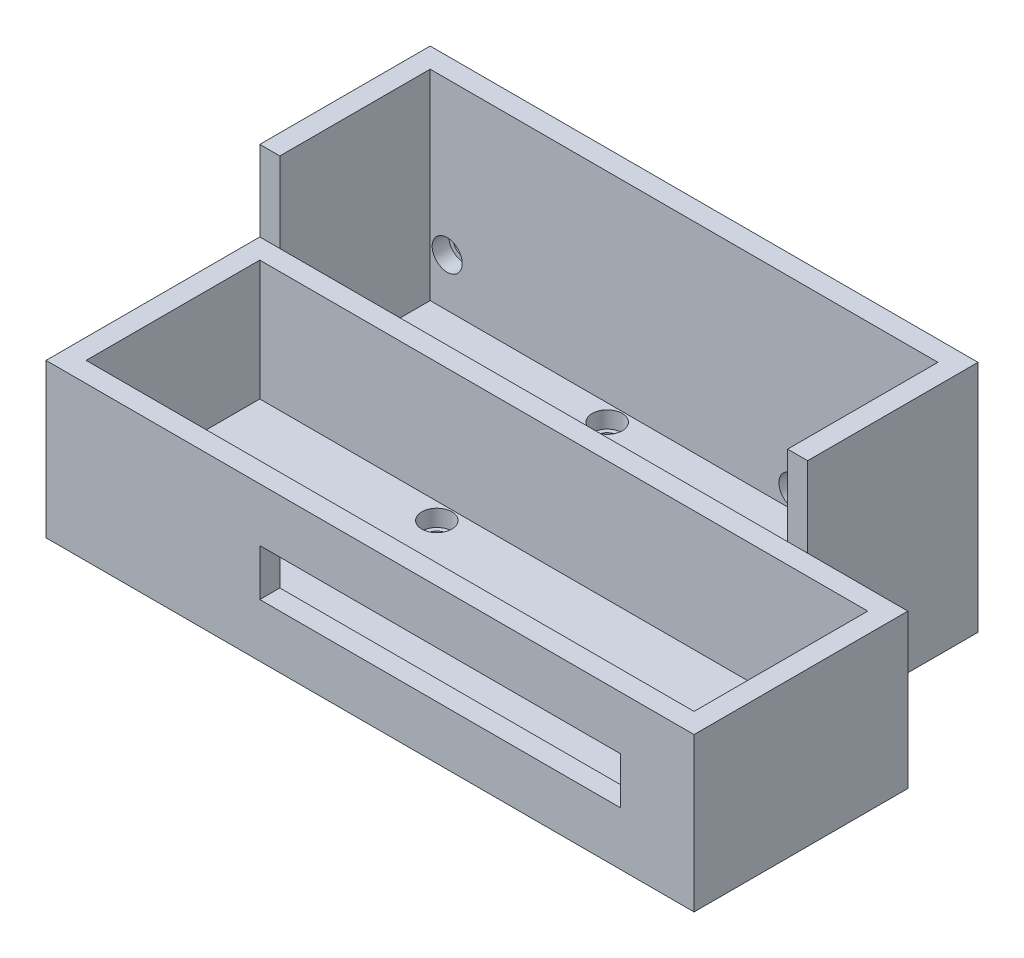
SolidWorks part; units mm, degrees
ref_plane "Front Plane" through (0, 0, 0) normal (0, 0, 1) x (1, 0, 0)
ref_plane "Top Plane" through (0, 0, 0) normal (0, 1, 0) x (1, 0, 0)
ref_plane "Right Plane" through (0, 0, 0) normal (1, 0, 0) x (0, 0, -1)
sketch "Sketch1" plane through (0, 0, 0) normal (0, 1, 0) x (1, 0, 0)
  line L1 (0, 0) -> (91, 0)
  line L2 (0, 0) -> (0, 26)
  line L3 (0, 26) -> (91, 26)
  line L4 (91, 0) -> (91, 26)
extrude "Boss-Extrude1" add sketch "Sketch1" along normal blind 5
sketch "Sketch2" plane through (0, 5, 0) normal (0, 1, 0) x (1, 0, 0)
  line L0 (0, 2.5) -> (29, 2.5) construction
  line L9 (29, 2.5) -> (29, 26) construction
  line L10 (91, 26) -> (0, 26) construction
  line L11 (29, 26) -> (29, 23.5) construction
  circle A0 centre (2.5, 2.5) radius 2.25
  circle A1 centre (88.5, 2.5) radius 2.25
  circle A2 centre (29, 23.5) radius 2.25
  dimension "D1" = 4.5
  dimension "D2" = 4.5
  dimension "D3" = 4.5
extrude "Cut-Extrude1" cut sketch "Sketch2" against normal blind 2.5
sketch "Sketch4" plane through (0, 2.5, 0) normal (0, 1, 0) x (1, 0, 0)
  circle A0 centre (2.5, 2.5) radius 1.6
  circle A1 centre (29, 23.5) radius 1.6
  circle A2 centre (88.5, 2.5) radius 1.6
  dimension "D1" = 3.2
  dimension "D2" = 3.2
  dimension "D3" = 3.2
extrude "Cut-Extrude3" cut sketch "Sketch4" against normal through all
sketch "Sketch5" plane through (0, 0, 0) normal (0, -1, 0) x (1, 0, 0)
  line L0 (-3, 0) -> (-3, -29) construction
  line L9 (-3, -29) -> (91, -29) construction
  line L10 (94, 3) -> (94, -26) construction
  line L11 (94, 3) -> (0, 3) construction
  line L13 (94, 3) -> (-3, 3)
  line L14 (94, 3) -> (94, -29)
  line L15 (94, -29) -> (-3, -29)
  line L16 (-3, 3) -> (-3, -29)
  line L17 (0, 0) -> (91, 0)
  line L18 (0, 0) -> (0, -26)
  line L19 (0, -26) -> (91, -26)
  line L20 (91, 0) -> (91, -26)
extrude "Boss-Extrude2" add sketch "Sketch5" against normal blind 23
sketch "Sketch6" plane through (0, 0, 3) normal (0, 0, 1) x (1, 0, 0)
  line L0 (-3, 0) -> (0, 0) construction
  line L1 (0, 0) -> (29, 0) construction
  line L2 (94, 0) -> (-3, 0) construction
  line L3 (29, 0) -> (83, 0) construction
  line L4 (83, 0) -> (83, 8) construction
  line L5 (83, 8) -> (83, 15) construction
  line L6 (83, 15) -> (29, 15) construction
  line L8 (29, 15) -> (83, 15)
  line L9 (29, 15) -> (29, 8)
  line L10 (29, 8) -> (83, 8)
  line L11 (83, 15) -> (83, 8)
  dimension "D1" = 8
  dimension "D2" = 7
extrude "Cut-Extrude4" cut sketch "Sketch6" against normal up to next
sketch "Sketch9" plane through (0, 0, -29) normal (0, 0, -1) x (-1, 0, 0)
  line L1 (0, 0) -> (-76, 0)
  line L2 (0, 0) -> (0, 5)
  line L3 (0, 5) -> (-76, 5)
  line L4 (-76, 0) -> (-76, 5)
extrude "Boss-Extrude3" add sketch "Sketch9" along normal blind 22.5
sketch "Sketch10" plane through (0, 5, 0) normal (0, 1, 0) x (1, 0, 0)
  line L0 (29, 23.5) -> (29, 49) construction
  circle A0 centre (29, 49) radius 2.25
  dimension "D1" = 4.5
extrude "Cut-Extrude5" cut sketch "Sketch10" against normal blind 2.5
sketch "Sketch11" plane through (0, 2.5, 0) normal (0, 1, 0) x (1, 0, 0)
  circle A0 centre (29, 49) radius 1.6
  dimension "D1" = 3.2
extrude "Cut-Extrude6" cut sketch "Sketch11" against normal through all
sketch "Sketch12" plane through (0, 0, 0) normal (0, -1, 0) x (1, 0, 0)
  line L1 (0, -29) -> (-3, -29)
  line L2 (0, -29) -> (0, -51.5)
  line L3 (0, -54.5) -> (-3, -54.5)
  line L4 (-3, -29) -> (-3, -54.5)
  line L5 (0, -54.5) -> (79, -54.5)
  line L7 (0, -51.5) -> (76, -51.5)
  line L8 (79, -54.5) -> (79, -51.5)
  line L10 (79, -51.5) -> (79, -29)
  line L11 (79, -29) -> (76, -29)
  line L12 (76, -51.5) -> (76, -29)
extrude "Boss-Extrude4" add sketch "Sketch12" against normal blind 35
sketch "Sketch13" plane through (79, 0, 0) normal (1, 0, 0) x (0, 0, -1)
  line L0 (29, 0) -> (31.5, 0) construction
  line L1 (54.5, 0) -> (29, 0) construction
  line L2 (31.5, 0) -> (31.5, 10) construction
  circle A0 centre (31.5, 10) radius 1.6
  dimension "D1" = 3.2
extrude "Cut-Extrude7" cut sketch "Sketch13" against normal up to next
sketch "Sketch14" plane through (0, 0, -54.5) normal (0, 0, -1) x (-1, 0, 0)
  line L0 (0, 0) -> (0, 5) construction
  line L1 (0, 5) -> (-76, 5) construction
  line L2 (-38, 5) -> (-38, 7.5) construction
  line L4 (-2.55, 7.5) -> (-2.55, 12.2) construction
  circle A0 centre (-54.45, 7.5) radius 1.6
  circle A1 centre (-2.55, 12.2) radius 1.6
  point P9 (-38, 7.5)
  dimension "D1" = 3.2
  dimension "D2" = 3.2
  dimension "D4" = 5.1
  dimension "D3" = 51.9
extrude "Cut-Extrude8" cut sketch "Sketch14" against normal up to next
sketch "Sketch16" plane through (0, 0, -51.5) normal (0, 0, 1) x (1, 0, 0)
  circle A0 centre (2.55, 12.2) radius 2.25
  circle A1 centre (54.45, 7.5) radius 2.25
  dimension "D1" = 4.5
  dimension "D2" = 4.5
extrude "Cut-Extrude10" cut sketch "Sketch16" against normal blind 2.5
sketch "Sketch17" plane through (0, 0, -54.5) normal (0, 0, -1) x (-1, 0, 0)
  circle A0 centre (-54.45, 7.5) radius 1.6
  circle A1 centre (-54.45, 7.5) radius 2.5
  circle A2 centre (-2.55, 12.2) radius 1.6
  circle A3 centre (-2.55, 12.2) radius 2.5
  dimension "D1" = 3.2
  dimension "D2" = 5
  dimension "D3" = 3.2
  dimension "D4" = 5
extrude "Boss-Extrude5" add sketch "Sketch17" along normal blind 1.3
sketch "Sketch18" plane through (76, 0, 0) normal (-1, 0, 0) x (0, 0, 1)
  circle A0 centre (-31.5, 10) radius 2.25
  dimension "D1" = 4.5
extrude "Cut-Extrude11" cut sketch "Sketch18" against normal blind 1.5
sketch "Sketch3" plane through (0, 2.5, 0) normal (0, 1, 0) x (1, 0, 0)
